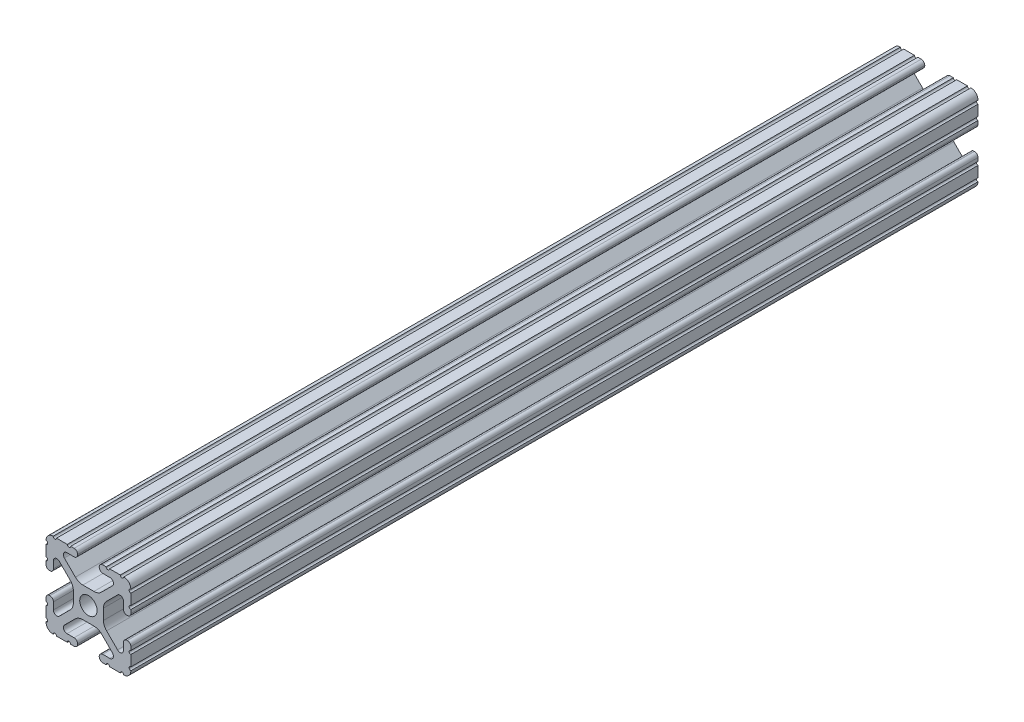
SolidWorks part; units mm, degrees
ref_plane "Front Plane" through (0, 0, 0) normal (0, 0, 1) x (1, 0, 0)
ref_plane "Top Plane" through (0, 0, 0) normal (0, 1, 0) x (1, 0, 0)
ref_plane "Right Plane" through (0, 0, 0) normal (1, 0, 0) x (0, 0, -1)
sketch "Sketch1" plane through (0, 0, 0) normal (0, 0, 1) x (1, 0, 0)
  line L88 (-7.1797, -8.6452) -> (-3.9523, -5.4237)
  line L89 (-1.7093, -4.4958) -> (1.7093, -4.4958)
  line L90 (3.9523, -5.4237) -> (7.1797, -8.6452)
  line L91 (6.4164, -10.4902) -> (4.2875, -10.4902)
  line L92 (3.2385, -11.5392) -> (3.2385, -11.651)
  line L93 (4.2875, -12.7) -> (5.3171, -12.7)
  line L94 (6.3331, -12.7) -> (9.5504, -12.7)
  line L95 (12.7, -9.5504) -> (12.7, -6.3331)
  line L96 (12.7, -5.3171) -> (12.7, -4.2875)
  line L97 (11.651, -3.2385) -> (11.5392, -3.2385)
  line L98 (10.4902, -4.2875) -> (10.4902, -6.4021)
  line L99 (8.7371, -7.1294) -> (5.441, -3.8408)
  line L100 (4.5085, -1.5932) -> (4.5085, 1.5932)
  line L101 (5.441, 3.8408) -> (8.7371, 7.1294)
  line L102 (10.4902, 6.4021) -> (10.4902, 4.2875)
  line L103 (11.5392, 3.2385) -> (11.651, 3.2385)
  line L104 (12.7, 4.2875) -> (12.7, 5.3171)
  line L105 (12.7, 6.3331) -> (12.7, 9.5504)
  line L106 (9.5504, 12.7) -> (6.3331, 12.7)
  line L107 (5.3171, 12.7) -> (4.2875, 12.7)
  line L108 (3.2385, 11.651) -> (3.2385, 11.5392)
  line L109 (4.2875, 10.4902) -> (6.4768, 10.4902)
  line L110 (7.207, 8.7244) -> (3.8983, 5.4232)
  line L111 (1.6558, 4.4958) -> (-1.6558, 4.4958)
  line L112 (-3.8983, 5.4232) -> (-7.207, 8.7244)
  line L113 (-6.4768, 10.4902) -> (-4.2875, 10.4902)
  line L114 (-3.2385, 11.5392) -> (-3.2385, 11.651)
  line L115 (-4.2875, 12.7) -> (-5.3171, 12.7)
  line L116 (-6.3331, 12.7) -> (-9.5504, 12.7)
  line L117 (-12.7, 9.5504) -> (-12.7, 6.3331)
  line L118 (-12.7, 5.3171) -> (-12.7, 4.2875)
  line L119 (-11.651, 3.2385) -> (-11.5392, 3.2385)
  line L120 (-10.4902, 4.2875) -> (-10.4902, 6.4021)
  line L121 (-8.7371, 7.1294) -> (-5.441, 3.8408)
  line L122 (-4.5085, 1.5932) -> (-4.5085, -1.5932)
  line L123 (-5.441, -3.8408) -> (-8.7371, -7.1294)
  line L124 (-10.4902, -6.4021) -> (-10.4902, -4.2875)
  line L125 (-11.5392, -3.2385) -> (-11.651, -3.2385)
  line L126 (-12.7, -4.2875) -> (-12.7, -5.3171)
  line L127 (-12.7, -6.3331) -> (-12.7, -9.5504)
  line L128 (-9.5504, -12.7) -> (-6.3331, -12.7)
  line L129 (-5.3171, -12.7) -> (-4.2875, -12.7)
  line L130 (-3.2385, -11.651) -> (-3.2385, -11.5392)
  line L131 (-4.2875, -10.4902) -> (-6.4164, -10.4902)
  circle A1 centre (0, 0) radius 2.6035
  arc A104 (-7.1797, -8.6452) -> (-6.4164, -10.4902) centre (-6.4164, -9.4098) ccw
  arc A105 (-1.7093, -4.4958) -> (-3.9523, -5.4237) centre (-1.7093, -7.6708) ccw
  arc A106 (3.9523, -5.4237) -> (1.7093, -4.4958) centre (1.7093, -7.6708) ccw
  arc A107 (6.4164, -10.4902) -> (7.1797, -8.6452) centre (6.4164, -9.4098) ccw
  arc A108 (4.2875, -10.4902) -> (3.2385, -11.5392) centre (4.2875, -11.5392) ccw
  arc A109 (3.2385, -11.651) -> (4.2875, -12.7) centre (4.2875, -11.651) ccw
  arc A110 (6.3331, -12.7) -> (5.3171, -12.7) centre (5.8251, -12.7) ccw
  arc A111 (10.5664, -12.6998) -> (9.5504, -12.7) centre (10.0584, -12.7) ccw
  arc A112 (10.5664, -12.6998) -> (12.6998, -10.5664) centre (10.5918, -10.5918) ccw
  arc A113 (12.7, -9.5504) -> (12.6998, -10.5664) centre (12.7, -10.0584) ccw
  arc A114 (12.7, -5.3171) -> (12.7, -6.3331) centre (12.7, -5.8251) ccw
  arc A115 (12.7, -4.2875) -> (11.651, -3.2385) centre (11.651, -4.2875) ccw
  arc A116 (11.5392, -3.2385) -> (10.4902, -4.2875) centre (11.5392, -4.2875) ccw
  arc A117 (8.7371, -7.1294) -> (10.4902, -6.4021) centre (9.4628, -6.4021) ccw
  arc A118 (4.5085, -1.5932) -> (5.441, -3.8408) centre (7.6835, -1.5932) ccw
  arc A119 (5.441, 3.8408) -> (4.5085, 1.5932) centre (7.6835, 1.5932) ccw
  arc A120 (10.4902, 6.4021) -> (8.7371, 7.1294) centre (9.4628, 6.4021) ccw
  arc A121 (10.4902, 4.2875) -> (11.5392, 3.2385) centre (11.5392, 4.2875) ccw
  arc A122 (11.651, 3.2385) -> (12.7, 4.2875) centre (11.651, 4.2875) ccw
  arc A123 (12.7, 6.3331) -> (12.7, 5.3171) centre (12.7, 5.8251) ccw
  arc A124 (12.6998, 10.5664) -> (12.7, 9.5504) centre (12.7, 10.0584) ccw
  arc A125 (12.6998, 10.5664) -> (10.5664, 12.6998) centre (10.5918, 10.5918) ccw
  arc A126 (9.5504, 12.7) -> (10.5664, 12.6998) centre (10.0584, 12.7) ccw
  arc A127 (5.3171, 12.7) -> (6.3331, 12.7) centre (5.8251, 12.7) ccw
  arc A128 (4.2875, 12.7) -> (3.2385, 11.651) centre (4.2875, 11.651) ccw
  arc A129 (3.2385, 11.5392) -> (4.2875, 10.4902) centre (4.2875, 11.5392) ccw
  arc A130 (7.207, 8.7244) -> (6.4768, 10.4902) centre (6.4768, 9.4563) ccw
  arc A131 (1.6558, 4.4958) -> (3.8983, 5.4232) centre (1.6558, 7.6708) ccw
  arc A132 (-3.8983, 5.4232) -> (-1.6558, 4.4958) centre (-1.6558, 7.6708) ccw
  arc A133 (-6.4768, 10.4902) -> (-7.207, 8.7244) centre (-6.4768, 9.4563) ccw
  arc A134 (-4.2875, 10.4902) -> (-3.2385, 11.5392) centre (-4.2875, 11.5392) ccw
  arc A135 (-3.2385, 11.651) -> (-4.2875, 12.7) centre (-4.2875, 11.651) ccw
  arc A136 (-6.3331, 12.7) -> (-5.3171, 12.7) centre (-5.8251, 12.7) ccw
  arc A137 (-10.5664, 12.6998) -> (-9.5504, 12.7) centre (-10.0584, 12.7) ccw
  arc A138 (-10.5664, 12.6998) -> (-12.6998, 10.5664) centre (-10.5918, 10.5918) ccw
  arc A139 (-12.7, 9.5504) -> (-12.6998, 10.5664) centre (-12.7, 10.0584) ccw
  arc A140 (-12.7, 5.3171) -> (-12.7, 6.3331) centre (-12.7, 5.8251) ccw
  arc A141 (-12.7, 4.2875) -> (-11.651, 3.2385) centre (-11.651, 4.2875) ccw
  arc A142 (-11.5392, 3.2385) -> (-10.4902, 4.2875) centre (-11.5392, 4.2875) ccw
  arc A143 (-8.7371, 7.1294) -> (-10.4902, 6.4021) centre (-9.4628, 6.4021) ccw
  arc A144 (-4.5085, 1.5932) -> (-5.441, 3.8408) centre (-7.6835, 1.5932) ccw
  arc A145 (-5.441, -3.8408) -> (-4.5085, -1.5932) centre (-7.6835, -1.5932) ccw
  arc A146 (-10.4902, -6.4021) -> (-8.7371, -7.1294) centre (-9.4628, -6.4021) ccw
  arc A147 (-10.4902, -4.2875) -> (-11.5392, -3.2385) centre (-11.5392, -4.2875) ccw
  arc A148 (-11.651, -3.2385) -> (-12.7, -4.2875) centre (-11.651, -4.2875) ccw
  arc A149 (-12.7, -6.3331) -> (-12.7, -5.3171) centre (-12.7, -5.8251) ccw
  arc A150 (-12.6998, -10.5664) -> (-12.7, -9.5504) centre (-12.7, -10.0584) ccw
  arc A151 (-12.6998, -10.5664) -> (-10.5664, -12.6998) centre (-10.5918, -10.5918) ccw
  arc A152 (-9.5504, -12.7) -> (-10.5664, -12.6998) centre (-10.0584, -12.7) ccw
  arc A153 (-5.3171, -12.7) -> (-6.3331, -12.7) centre (-5.8251, -12.7) ccw
  arc A154 (-4.2875, -12.7) -> (-3.2385, -11.651) centre (-4.2875, -11.651) ccw
  arc A155 (-3.2385, -11.5392) -> (-4.2875, -10.4902) centre (-4.2875, -11.5392) ccw
extrude "Boss-Extrude1" add sketch "Sketch1" along normal mid plane 609.6
sketch "Sketch2" plane through (-12.7, 0, 0) normal (-1, 0, 0) x (0, 0, 1)
  line L0 (-38.0019, 12.6998) -> (-38.0019, -14.659) construction
  line L1 (304.8, 12.6998) -> (-304.8, 12.6998) construction
  line L2 (-38.0019, 12.7) -> (-38.0019, 10.5918) construction
  line L4 (-51.1624, 15.2274) -> (307.2081, 15.2274)
  line L5 (307.2081, 15.2274) -> (307.2081, -14.659)
  line L6 (307.2081, -14.659) -> (-51.1624, -14.659)
  line L7 (-51.1624, 0) -> (-51.1624, 24.8234) construction
  line L8 (-51.1624, 10.5918) -> (-51.1624, -10.5918) construction
  line L9 (-51.1624, 15.2274) -> (-51.1624, -14.659)
extrude "Cut-Extrude1" cut sketch "Sketch2" against normal blind 29.464 and the other way blind 2.794
